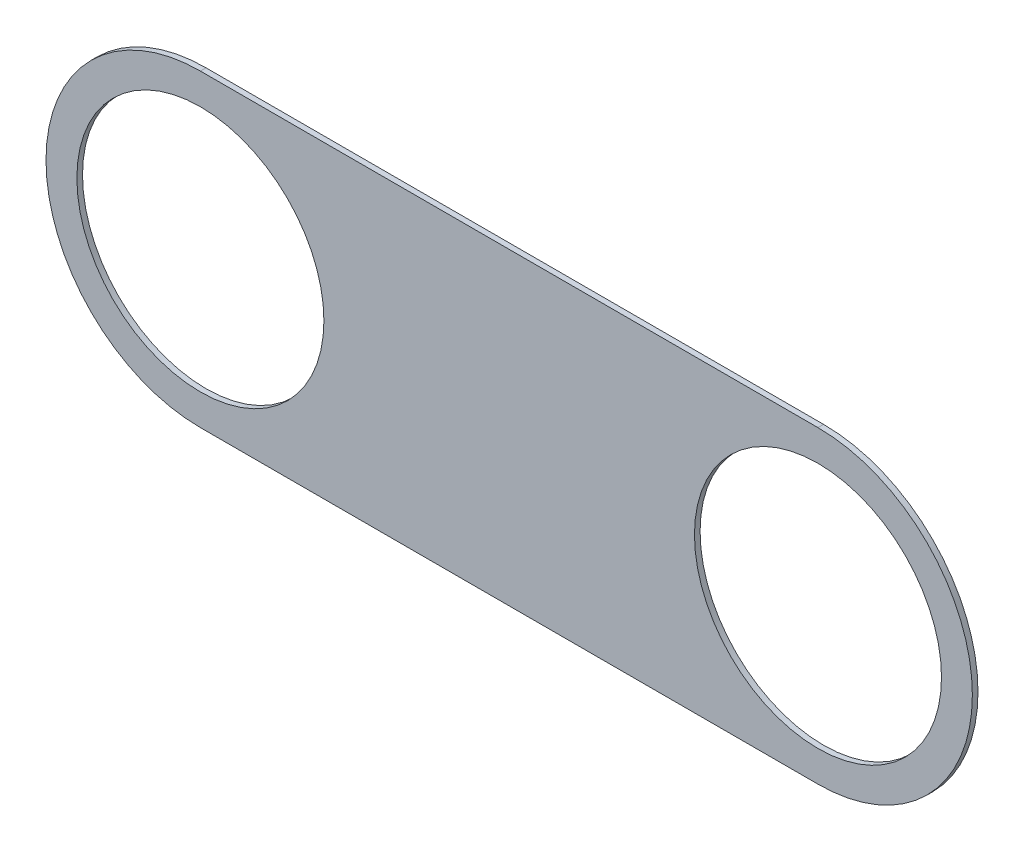
SolidWorks part; units mm, degrees
material "Plain Carbon Steel"
ref_plane "Front Plane" through (0, 0, 0) normal (0, 0, 1) x (1, 0, 0)
ref_plane "Top Plane" through (0, 0, 0) normal (0, 1, 0) x (1, 0, 0)
ref_plane "Right Plane" through (0, 0, 0) normal (1, 0, 0) x (0, 0, -1)
sketch "Sketch2" plane through (0, 0, 0) normal (0, 0, 1) x (1, 0, 0)
  line L0 (-63.5, 0) -> (63.5, 0) construction
  line L1 (-63.5, 31.75) -> (63.5, 31.75)
  line L2 (-63.5, -31.75) -> (63.5, -31.75)
  arc A0 (-63.5, 31.75) -> (-63.5, -31.75) centre (-63.5, 0) ccw
  arc A1 (63.5, -31.75) -> (63.5, 31.75) centre (63.5, 0) ccw
  circle A2 centre (-63.5, 0) radius 25.4
  circle A3 centre (63.5, 0) radius 25.4
  point P3 (0, 0)
  dimension "D1" = 50.8
  dimension "D2" = 50.8
  dimension "D4" = 6.35
  dimension "D3" = 127
extrude "Boss-Extrude1" add sketch "Sketch2" along normal blind 1.1582
